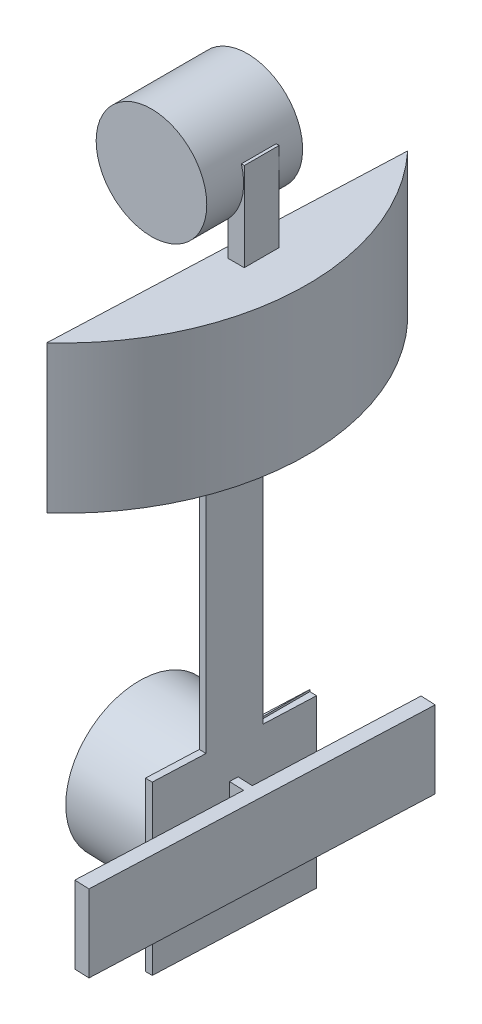
SolidWorks part; units mm, degrees
ref_plane "Front Plane" through (0, 0, 0) normal (0, 0, 1) x (1, 0, 0)
ref_plane "Top Plane" through (0, 0, 0) normal (0, 1, 0) x (1, 0, 0)
ref_plane "Right Plane" through (0, 0, 0) normal (1, 0, 0) x (0, 0, -1)
sketch "Sketch1" plane through (0, 0, 0) normal (0, 1, 0) x (1, 0, 0)
  line L0 (24.0966, 22.5467) -> (22.1593, -24.4533)
  arc A0 (22.1593, -24.4533) -> (24.0966, 22.5467) centre (0, 0) ccw
extrude "Boss-Extrude1" add sketch "Sketch1" along normal blind 20 contours A0 L0
sketch "Sketch2" plane through (0, 0, 0) normal (0, -1, 0) x (1, 0, 0)
  line L0 (22.1593, 24.4533) -> (24.0966, -22.5467)
  line L1 (23.128, 23.5393) -> (24.9868, -21.556)
  arc A0 (24.0966, -22.5467) -> (24.9868, -21.556) centre (0, 0) ccw
  arc A1 (23.128, 23.5393) -> (22.1593, 24.4533) centre (0, 0) ccw
extrude "Boss-Extrude2" add sketch "Sketch2" along normal blind 60 contours L1 A0 L0 A1
sketch "Sketch3" plane through (23.128, 0, 0.9533) normal (-0.9992, 0, -0.0412) x (-0.0412, 0, 0.9992)
  line L0 (23.52, -60) -> (-23.52, -60) construction
  circle A0 centre (0, -47) radius 10
  dimension "D1" = 20
  dimension "D2" = 13
extrude "Boss-Extrude3" add sketch "Sketch3" along normal blind 12
sketch "Sketch6" plane through (24.0574, 0, 0.9916) normal (0.9992, 0, 0.0412) x (0.0412, 0, -0.9992)
  line L0 (-22.5668, -60) -> (22.5668, -60) construction
  circle A0 centre (0, -47) radius 1.5
  dimension "D1" = 3
  dimension "D2" = 13
extrude "Boss-Extrude4" add sketch "Sketch6" along normal blind 3
sketch "Sketch7" plane through (24.0574, 0, 0.9916) normal (0.9992, 0, 0.0412) x (0.0412, 0, -0.9992)
  line L0 (-22.5668, -60) -> (-22.5668, 0) construction
  line L1 (-22.5668, -42.0372) -> (22.5668, -42.0372)
  line L2 (-22.5668, -42.0372) -> (-22.5668, -52.4989)
  line L3 (-22.5668, -52.4989) -> (22.5668, -52.4989)
  line L4 (22.5668, -42.0372) -> (22.5668, -52.4989)
  line L5 (22.5668, -60) -> (22.5668, 0) construction
extrude "Boss-Extrude5" add sketch "Sketch7" along normal blind 4
sketch "Sketch9" plane through (-0.9294, 0, 22.5476) normal (-0.0412, 0, 0.9992) x (0.9992, 0, 0.0412)
  line L0 (28.0778, -42.0372) -> (24.0778, -42.0372) construction
  line L1 (24.0778, -52.4989) -> (26.0778, -52.4989)
  line L2 (24.0778, -52.4989) -> (24.0778, -42.0372)
  line L3 (24.0778, -42.0372) -> (26.0778, -42.0372)
  line L4 (26.0778, -52.4989) -> (26.0778, -42.0372)
  dimension "D1" = 2
extrude "Cut-Extrude2" cut sketch "Sketch9" against normal blind 22
sketch "Sketch10" plane through (0.9294, 0, -22.5476) normal (0.0412, 0, -0.9992) x (-0.9992, 0, -0.0412)
  line L0 (-28.0778, -52.4989) -> (-24.0778, -52.4989) construction
  line L1 (-24.0778, -42.0372) -> (-26.0778, -42.0372)
  line L2 (-24.0778, -42.0372) -> (-24.0778, -52.4989)
  line L3 (-24.0778, -52.4989) -> (-26.0778, -52.4989)
  line L4 (-26.0778, -42.0372) -> (-26.0778, -52.4989)
  dimension "D1" = 2
extrude "Cut-Extrude3" cut sketch "Sketch10" against normal blind 22
sketch "Sketch16" plane through (0, -60, 0) normal (0, -1, 0) x (1, 0, 0)
  line L0 (22.1593, 24.4533) -> (22.6886, 11.6122)
  line L1 (23.128, 23.5393) -> (23.6196, 11.6122)
  line L2 (22.6886, 11.6122) -> (23.6196, 11.6122)
  arc A0 (23.128, 23.5393) -> (22.1593, 24.4533) centre (0, 0) ccw
extrude "Cut-Extrude7" cut sketch "Sketch16" against normal blind 60
sketch "Sketch19" plane through (0, -60, 0) normal (0, -1, 0) x (1, 0, 0)
  line L0 (23.5711, -9.7978) -> (24.5021, -9.7978)
  line L1 (22.6886, 11.6122) -> (24.0966, -22.5467) construction
  line L2 (23.6196, 11.6122) -> (24.9868, -21.556) construction
  line L3 (24.5021, -9.7978) -> (24.9868, -21.556)
  line L4 (23.5711, -9.7978) -> (24.0966, -22.5467)
  arc A0 (24.0966, -22.5467) -> (24.9868, -21.556) centre (0, 0) ccw construction
  arc A1 (24.0966, -22.5467) -> (24.9868, -21.556) centre (0, 0) ccw
extrude "Cut-Extrude8" cut sketch "Sketch19" against normal blind 60
sketch "Sketch20" plane through (0, 0, -9.7978) normal (0, 0, -1) x (-1, 0, 0)
  line L0 (-24.5021, 0) -> (-24.5021, -60) construction
  line L1 (-23.5711, 0) -> (-24.5021, 0)
  line L2 (-23.5711, 0) -> (-23.5711, -37.4016)
  line L3 (-23.5711, -37.4016) -> (-24.5021, -37.4016)
  line L4 (-24.5021, 0) -> (-24.5021, -37.4016)
extrude "Cut-Extrude9" cut sketch "Sketch20" against normal blind 7
sketch "Sketch21" plane through (23.5711, 0, 0) normal (1, 0, 0) x (0, 0, -1)
  line L0 (9.7978, 0) -> (9.7978, -37.4016) construction
  line L1 (2.7978, 0) -> (9.7978, 0)
  line L2 (2.7978, 0) -> (2.7978, -37.1431)
  line L3 (2.7978, -37.1431) -> (9.7978, -37.1431)
  line L4 (9.7978, 0) -> (9.7978, -37.1431)
extrude "Cut-Extrude10" cut sketch "Sketch21" against normal blind 7
sketch "Sketch24" plane through (24.0574, 0, 0.9916) normal (0.9992, 0, 0.0412) x (0.0412, 0, -0.9992)
  line L0 (-10.6296, 0) -> (-10.6296, -60) construction
  line L1 (-10.6296, -37.2882) -> (-3.6296, -37.2882)
  line L2 (-10.6296, -37.2882) -> (-10.6296, 0)
  line L3 (-10.6296, 0) -> (-3.6296, 0)
  line L4 (-3.6296, -37.2882) -> (-3.6296, 0)
  line L5 (-10.6296, 0) -> (3.7927, 0) construction
  dimension "D1" = 7
extrude "Cut-Extrude11" cut sketch "Sketch24" against normal blind 7
sketch "Sketch25" plane through (0, 0, 11.6122) normal (0, 0, 1) x (1, 0, 0)
  line L0 (23.6196, -37.2882) -> (23.6196, -60) construction
  line L1 (22.6886, 0) -> (23.6196, 0)
  line L2 (22.6886, 0) -> (22.6886, -37.2882)
  line L3 (22.6886, -37.2882) -> (23.6196, -37.2882)
  line L4 (23.6196, 0) -> (23.6196, -37.2882)
  line L5 (23.6196, 0) -> (23.6196, -37.2882) construction
extrude "Cut-Extrude12" cut sketch "Sketch25" against normal blind 7
sketch "Sketch31" plane through (0, 20, 0) normal (0, 1, 0) x (1, 0, 0)
  line L1 (24.5635, 2.4728) -> (26.7372, 2.4728)
  line L2 (24.5635, 2.4728) -> (24.5635, -2.2529)
  line L3 (24.5635, -2.2529) -> (26.7372, -2.2529)
  line L4 (26.7372, 2.4728) -> (26.7372, -2.2529)
extrude "Boss-Extrude8" add sketch "Sketch31" along normal blind 12
sketch "Sketch32" plane through (0, 0, 2.2529) normal (0, 0, 1) x (1, 0, 0)
  circle A0 centre (19.1506, 29.8602) radius 7.5
  dimension "D1" = 15
extrude "Boss-Extrude12" add sketch "Sketch32" along normal blind 5
sketch "Sketch35" plane through (0, 0, 2.2529) normal (0, 0, -1) x (-1, 0, 0)
  circle A0 centre (-19.1506, 29.8602) radius 7.5
extrude "Boss-Extrude14" add sketch "Sketch35" along normal blind 8
